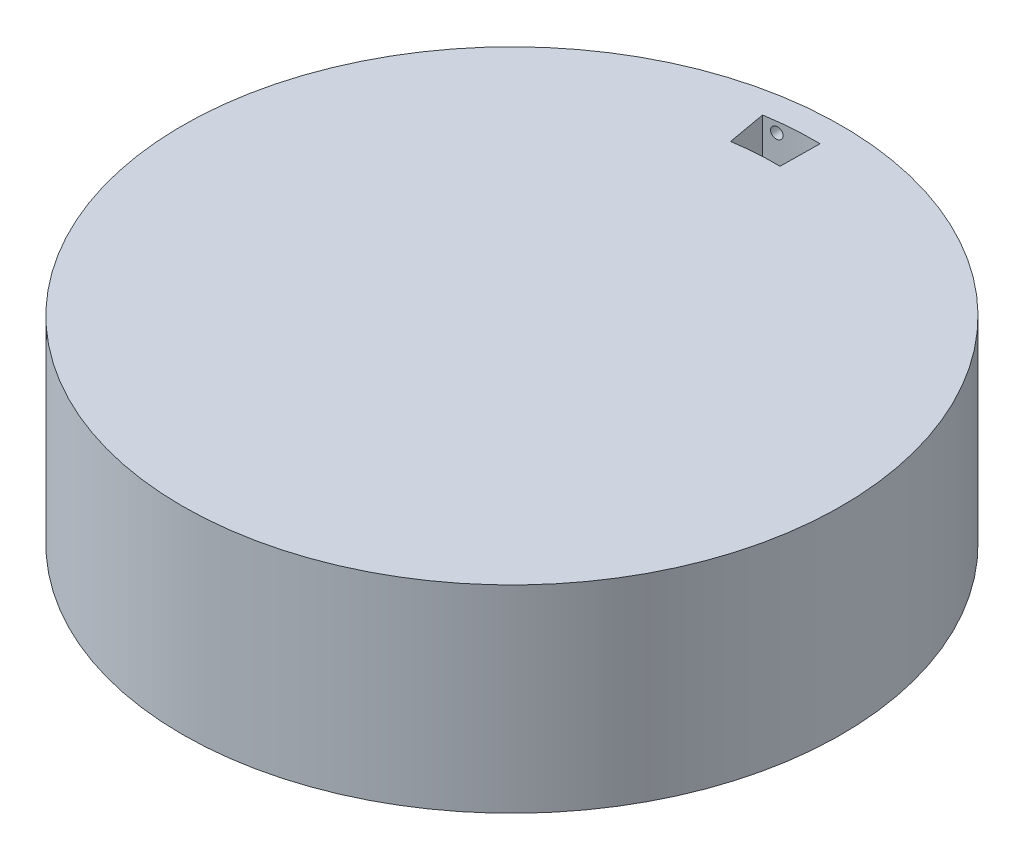
SolidWorks part; units mm, degrees
ref_plane "Front Plane" through (0, 0, 0) normal (0, 0, 1) x (1, 0, 0)
ref_plane "Top Plane" through (0, 0, 0) normal (0, 1, 0) x (1, 0, 0)
ref_plane "Right Plane" through (0, 0, 0) normal (1, 0, 0) x (0, 0, -1)
sketch "Sketch1" plane through (0, 0, 0) normal (0, 1, 0) x (1, 0, 0)
  circle A0 centre (0, 0) radius 31.75
extrude "Boss-Extrude1" add sketch "Sketch1" along normal blind 19.05
sketch "Sketch2" plane through (0, 19.05, 0) normal (0, 1, 0) x (1, 0, 0)
  line L0 (0.4319, 25.3963) -> (0.4816, 29.206)
  line L1 (-4.0214, 25.0796) -> (-4.6853, 28.8318)
  arc A0 (0.4816, 29.206) -> (-4.6853, 28.8318) centre (0, 0) ccw
  arc A1 (0.4319, 25.3963) -> (-4.0214, 25.0796) centre (0, 0) ccw
  circle A2 centre (0, 0) radius 31.75 construction
extrude "Cut-Extrude1" cut sketch "Sketch2" against normal blind 5.08
ref_plane "Plane2" through (-1.7948, 0, -25.238) normal (-0.0709, 0, -0.9975) x (-0.9975, 0, 0.0709)
sketch "Sketch4" plane through (-1.7948, 0, -25.238) normal (-0.0709, 0, -0.9975) x (-0.9975, 0, 0.0709)
  line L0 (2.2322, 19.05) -> (-2.2322, 19.05)
  line L1 (2.2322, 19.05) -> (1.4159, 18.0771)
  circle A0 centre (1.4159, 18.0771) radius 0.5397
  dimension "D1" = 50
extrude "Cut-Extrude2" cut sketch "Sketch4" against normal blind 1.524 and the other way through all
